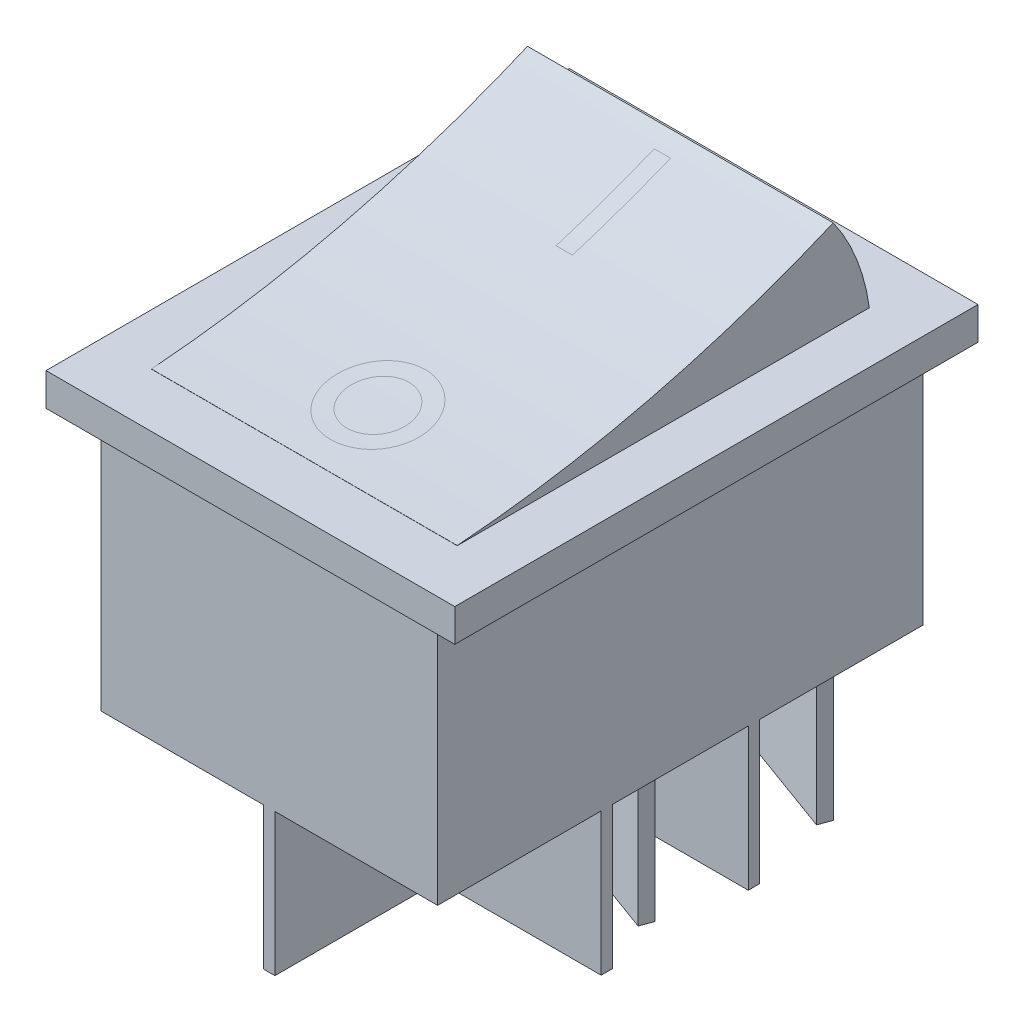
SolidWorks part; units mm, degrees
ref_plane "FRONT" through (0, 0, 0) normal (0, 0, 1) x (1, 0, 0)
ref_plane "TOP" through (0, 0, 0) normal (0, 1, 0) x (1, 0, 0)
ref_plane "RIGHT" through (0, 0, 0) normal (1, 0, 0) x (0, 0, -1)
sketch "Sketch1" plane through (0, 0, 0) normal (0, 0, 1) x (1, 0, 0)
  line L0 (12.5, 26.2) -> (-12.5, 26.2)
  line L1 (-12.5, 26.2) -> (-12.5, 24.2)
  line L2 (-12.5, 24.2) -> (-10.3, 24.2)
  line L3 (-10.3, 24.2) -> (-10.3, 0)
  line L4 (-10.3, 0) -> (10.3, 0)
  line L5 (0, 26.2) -> (0, 0) construction
  line L6 (10.3, 24.2) -> (10.3, 0)
  line L7 (12.5, 24.2) -> (10.3, 24.2)
  line L8 (12.5, 26.2) -> (12.5, 24.2)
  dimension "D1" = 25
  dimension "D2" = 20.6
  dimension "D3" = 2
  dimension "D4" = 26.2
extrude "Extrude1" add sketch "Sketch1" along normal mid plane 29.7
sketch "Sketch2" plane through (0, 0, 14.85) normal (0, 0, 1) x (1, 0, 0)
  line L1 (-12.5, 26.2) -> (12.5, 26.2)
  line L2 (-12.5, 26.2) -> (-12.5, 24.2)
  line L3 (-12.5, 24.2) -> (12.5, 24.2)
  line L4 (12.5, 26.2) -> (12.5, 24.2)
extrude "Extrude2" add sketch "Sketch2" along normal blind 1.15
mirror "Mirror1" about plane through (0, 0, 0) normal (0, 0, 1) of "Extrude2"
sketch "Sketch4" plane through (0, 0, 0) normal (1, 0, 0) x (0, 0, -1)
  line L0 (-12.7, 26.2) -> (-12.7, 26.21)
  line L1 (-16, 26.2) -> (16, 26.2) construction
  line L2 (-12.7, 26.2) -> (12.5, 26.2)
  line L3 (-16, 24.2) -> (-16, 26.2) construction
  line L5 (-16, 26.2) -> (16, 26.2) construction
  line L6 (16, 24.2) -> (16, 26.2) construction
  line L7 (0, 0) -> (0, 31.2367) construction
  arc A0 (-12.7, 26.21) -> (10.3, 31.8) centre (-18.2122, 99.0016) ccw
  arc A1 (10.3, 31.8) -> (12.5, 26.2) centre (0, 24.5214) cw
  dimension "D6" = 73
  dimension "D1" = 3.3
  dimension "D2" = 3.5
  dimension "D3" = 0.01
  dimension "D4" = 5.6
  dimension "D5" = 5.7
extrude "Extrude4" add sketch "Sketch4" along normal mid plane 18.7
sketch "Sketch5" plane through (0, 0, 0) normal (0, -1, 0) x (1, 0, 0)
  line L0 (0, 0) -> (0, 6.2202) construction
  line L1 (0, 0) -> (4.408, 0) construction
  line L2 (10.3, 14.85) -> (10.3, -14.85) construction
  line L3 (10.3, 14.85) -> (0.35, 14.85)
  line L4 (10.3, 14.85) -> (10.3, 4.85)
  line L5 (10.3, 4.85) -> (0.35, 4.85)
  line L6 (0.35, 14.85) -> (0.35, 4.85)
  line L7 (10.3, 4.15) -> (0.35, 4.15)
  line L8 (10.3, 4.15) -> (10.3, -4.15)
  line L9 (10.3, -4.15) -> (0.35, -4.15)
  line L10 (0.35, 4.15) -> (0.35, -4.15)
  line L11 (-0.35, 14.85) -> (-0.35, 4.85)
  line L12 (-10.3, 4.85) -> (-0.35, 4.85)
  line L13 (-10.3, 14.85) -> (-10.3, 4.85)
  line L14 (-10.3, 14.85) -> (-0.35, 14.85)
  line L15 (-10.3, -14.85) -> (-0.35, -14.85)
  line L16 (-10.3, -14.85) -> (-10.3, -4.85)
  line L17 (-10.3, -4.85) -> (-0.35, -4.85)
  line L18 (-0.35, -14.85) -> (-0.35, -4.85)
  line L19 (0.35, -14.85) -> (0.35, -4.85)
  line L20 (10.3, -4.85) -> (0.35, -4.85)
  line L21 (10.3, -14.85) -> (10.3, -4.85)
  line L22 (10.3, -14.85) -> (0.35, -14.85)
  line L23 (-0.35, 4.15) -> (-0.35, -4.15)
  line L24 (-10.3, -4.15) -> (-0.35, -4.15)
  line L25 (-10.3, 4.15) -> (-10.3, -4.15)
  line L26 (-10.3, 4.15) -> (-0.35, 4.15)
  dimension "D1" = 0.7
  dimension "D2" = 0.7
  dimension "D3" = 8.3
extrude "Cut-Extrude1" cut sketch "Sketch5" against normal blind 8.7
sketch "Sketch6" plane through (0, 0, 0) normal (0, 1, 0) x (1, 0, 0)
  line L0 (0, 0) -> (0, 18.021) construction
  line L1 (-0.5, 9.2) -> (0.5, 9.2)
  line L2 (-0.5, 9.2) -> (-0.5, 3.2)
  line L3 (-0.5, 3.2) -> (0.5, 3.2)
  line L4 (0.5, 9.2) -> (0.5, 3.2)
  line L5 (9.35, 10.3) -> (-9.35, 10.3) construction
  line L6 (9.35, -12.7) -> (-9.35, -12.7) construction
  circle A0 centre (0, -8.2) radius 1.9 construction
  circle A1 centre (0, -8.2) radius 2.9 construction
  dimension "D4" = 5.8
  dimension "D5" = 1
  dimension "D1" = 1
  dimension "D2" = 6
  dimension "D3" = 1.1
  dimension "D6" = 4.5
split line "Split Line3"
sketch "Sketch7" plane through (0, 0, 0) normal (0, 1, 0) x (1, 0, 0)
  line L0 (0, 0) -> (0, -14.0762) construction
  line L3 (-0.0005, -5.3) -> (-0.0005, -6.3)
  line L5 (0.0005, -5.3) -> (0.0005, -6.3)
  circle A0 centre (0, -8.2) radius 1.9 construction
  arc A1 (-0.0005, -6.3) -> (0.0005, -6.3) centre (0, -8.2) ccw
  circle A2 centre (0, -8.2) radius 2.9 construction
  arc A3 (-0.0005, -5.3) -> (0.0005, -5.3) centre (0, -8.2) ccw
  dimension "D1" = 0.001
split line "Split Line10"
sketch "Sketch9" plane through (0, 8.7, 0) normal (0, -1, 0) x (1, 0, 0)
  line L0 (-8.1456, -13.2057) -> (-2.2255, -11.0509)
  line L1 (-2.2255, -11.0509) -> (-2.4991, -10.2992)
  line L2 (-2.4991, -10.2992) -> (-8.4192, -12.4539)
  line L3 (-8.4192, -12.4539) -> (-8.1456, -13.2057)
  line L4 (-10.3, 14.85) -> (-10.3, -14.85) construction
  line L5 (2.6786, -13.2057) -> (8.5986, -11.0509)
  line L6 (8.5986, -11.0509) -> (8.325, -10.2992)
  line L7 (8.325, -10.2992) -> (2.405, -12.4539)
  line L8 (2.405, -12.4539) -> (2.6786, -13.2057)
  line L9 (-8.2417, -2.3925) -> (-2.3216, -0.2378)
  line L10 (-2.3216, -0.2378) -> (-2.5953, 0.5139)
  line L11 (-2.5953, 0.5139) -> (-8.5153, -1.6408)
  line L12 (-8.5153, -1.6408) -> (-8.2417, -2.3925)
  line L13 (2.5825, -2.3925) -> (8.5025, -0.2378)
  line L14 (8.5025, -0.2378) -> (8.2289, 0.5139)
  line L15 (8.2289, 0.5139) -> (2.3088, -1.6408)
  line L16 (2.3088, -1.6408) -> (2.5825, -2.3925)
  dimension "D1" = 0.8
  dimension "D2" = 6.3
  dimension "D3" = 70
extrude "Extrude5" add sketch "Sketch9" along normal blind 9.3
